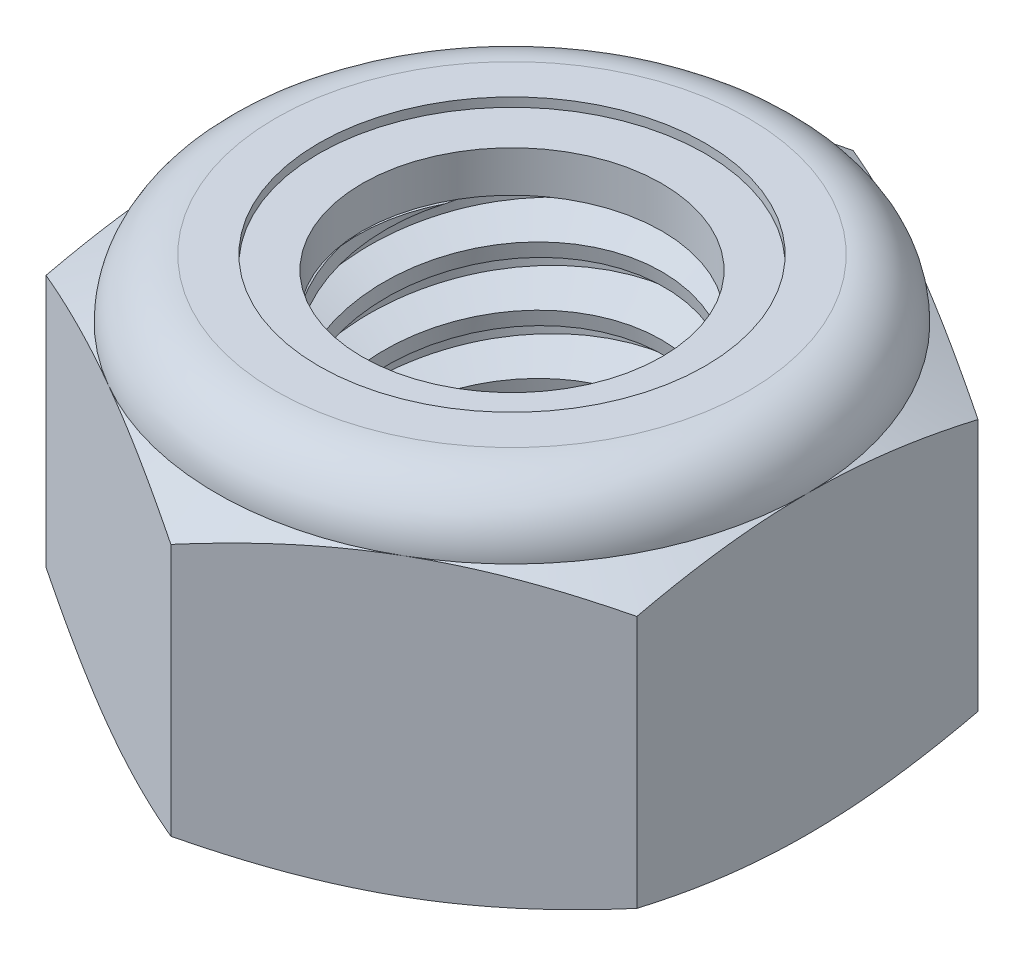
SolidWorks part; units mm, degrees
ref_plane "Front" through (0, 0, 0) normal (0, 0, 1) x (1, 0, 0)
ref_plane "Top" through (0, 0, 0) normal (0, 1, 0) x (1, 0, 0)
ref_plane "Right" through (0, 0, 0) normal (1, 0, 0) x (0, 0, -1)
sketch "Sketch1" plane through (0, 0, 0) normal (0, 1, 0) x (1, 0, 0)
  line L1 (0, 5.7735) -> (-5, 2.8868)
  line L2 (-5, 2.8868) -> (-5, -2.8868)
  line L3 (-5, -2.8868) -> (0, -5.7735)
  line L4 (0, -5.7735) -> (5, -2.8868)
  line L5 (5, -2.8868) -> (5, 2.8868)
  line L6 (5, 2.8868) -> (0, 5.7735)
  circle A0 centre (0, 0) radius 5 construction
  dimension "Hex Flats" = 10
extrude "Extrude1" add sketch "Sketch1" along normal blind 6
sketch "Sketch2" plane through (0, 0, 0) normal (1, 0, 0) x (0, 0, -1)
  line L0 (-3, 0) -> (-3, 6) construction
  line L1 (0, 0) -> (3, 0)
  line L2 (0, 0) -> (0, 6)
  line L3 (0, 6) -> (3, 6)
  line L4 (3, 0) -> (3, 6)
  line L5 (-2.8868, 6) -> (2.8868, 6) construction
  line L7 (0, -3) -> (0, 0) construction
  dimension "Thread Dia" = 6
revolve "Revolve1" add sketch "Sketch2" angle 360 about L7
sketch "Sketch3" plane through (0, 0, 0) normal (1, 0, 0) x (0, 0, -1)
  line L0 (3, 6) -> (-3, 6) construction
  line L1 (-3, 6) -> (-3, 5) construction
  line L2 (-3, 5) -> (3, 6) construction
  line L3 (3, 6) -> (3.0205, 5.8767) construction
  line L4 (3.0205, 5.8767) -> (3.1644, 5.0136)
  line L5 (3.1644, 5.0136) -> (2.5791, 5.2329)
  line L6 (2.5791, 5.2329) -> (2.538, 5.4795)
  line L7 (2.538, 5.4795) -> (3.0205, 5.8767)
  line L8 (2.5586, 5.3562) -> (3.0925, 5.4452) construction
  line L9 (3, 6) -> (3, 5.4297) construction
  line L10 (3, 5.4297) -> (-3, 4.4297) construction
  line L11 (-3, 4.4297) -> (-3, 5) construction
  line L12 (-0.1784, 6) -> (0.1784, 3.8595) construction
  line L13 (-3, 0) -> (-3, 6) construction
  line L14 (0, 6) -> (3, 6) construction
  line L15 (3, 0) -> (3, 6) construction
  point P13 (0, 4.9297)
  dimension "D1" = 0.125
  dimension "D2" = 0.25
  dimension "Thread Pitch" = 1
  dimension "D4" = 60
  dimension "D5" = 1
revolve "Cut-Revolve1" cut sketch "Sketch3" angle 360 about L12
pattern_linear "LPattern1" count 6 spacing 1 along (0, -1, 0) count 2 spacing 1 along (0, 1, 0) of "Cut-Revolve1"
sketch "Sketch4" plane through (0, 0, 0) normal (1, 0, 0) x (0, 0, -1)
  line L0 (0, 6) -> (3, 6)
  line L1 (3, 6) -> (2.538, 5.7846)
  line L2 (2.538, 5.7846) -> (2.538, 0.2154)
  line L3 (2.538, 0.2154) -> (3, 0)
  line L4 (3, 0) -> (0, 0)
  line L5 (0, 0) -> (0, 6)
  line L6 (3, 0) -> (3, 6) construction
  line L7 (0, 6) -> (3, 6) construction
  line L8 (0, 0) -> (3, 0) construction
  line L9 (0, 0) -> (0, 6) construction
  line L10 (0, 6) -> (0, 6.5097) construction
  dimension "D1" = 25
revolve "Cut-Revolve2" cut sketch "Sketch4" angle 360 about L10
combine bodies "Combine1" operation type subtract main body 112 bodies to subtract 111
sketch "Sketch5" plane through (0, 0, 0) normal (1, 0, 0) x (0, 0, -1)
  line L0 (0, 0) -> (5, 0)
  line L1 (5, 0) -> (5.7735, 0.3607)
  line L2 (5.7735, 0.3607) -> (5.7735, 4.6393)
  line L3 (5.7735, 4.6393) -> (5, 5)
  line L4 (4, 6) -> (4, 7.27)
  line L5 (4, 7.27) -> (7.0435, 7.27)
  line L6 (7.0435, 7.27) -> (7.0435, -1.27)
  line L7 (7.0435, -1.27) -> (0, -1.27)
  line L8 (0, -1.27) -> (0, 0)
  line L9 (5, 5) -> (5, 0) construction
  line L10 (0, 0) -> (3, 0) construction
  line L13 (5.7735, 2.5) -> (7.0435, 2.5) construction
  line L14 (5.7735, 6) -> (5.7735, 0) construction
  line L15 (0, 0) -> (0, 7.27) construction
  line L20 (0, 7.27) -> (4, 7.27) construction
  line L22 (0, 6) -> (3, 6) construction
  arc A0 (5, 5) -> (4, 6) centre (4, 5) ccw
  dimension "D1" = 25
  dimension "D2" = 1.27
  dimension "D3" = 6
  dimension "D4" = 1
revolve "Cut-Revolve3" cut sketch "Sketch5" angle 360 about L15
sketch "Sketch6" plane through (0, 0, 0) normal (1, 0, 0) x (0, 0, -1)
  line L0 (0, 5) -> (4.8476, 5)
  line L1 (4, 5.8476) -> (3.269, 5.8476)
  line L2 (0, 7.27) -> (0, 5)
  line L3 (3.269, 7.27) -> (0, 7.27)
  line L4 (0, 7.27) -> (4, 7.27) construction
  line L5 (0, 0) -> (0, 7.27) construction
  line L6 (0, 7.27) -> (0, 44.323) construction
  line L7 (3.269, 5.8476) -> (3.269, 7.27)
  line L8 (4, 6) -> (4, 5.8476) construction
  line L9 (3.269, 5.8476) -> (2.538, 5.8476) construction
  line L10 (2.538, 5.8476) -> (2.538, 5.7846) construction
  arc A0 (4.8476, 5) -> (4, 5.8476) centre (4, 5) ccw
  arc A1 (5, 5) -> (4, 6) centre (4, 5) ccw construction
  dimension "D1" = 0.1524
revolve "Cut-Revolve4" cut sketch "Sketch6" angle 360 about L6
sketch "Sketch7" plane through (0, 0, 0) normal (1, 0, 0) x (0, 0, -1)
  line L0 (2.538, 5.0762) -> (4.7676, 5.0762)
  line L1 (4, 5.7714) -> (2.538, 5.7714)
  line L2 (2.538, 5.7714) -> (2.538, 5.0762)
  line L3 (2.538, 5.0762) -> (0, 5.0762) construction
  line L4 (0, 5.0762) -> (0, 5.7714) construction
  line L5 (0, 5.7714) -> (2.538, 5.7714) construction
  line L6 (2.538, 5.0762) -> (2.538, 5) construction
  line L7 (0, 5) -> (4.8476, 5) construction
  line L8 (4, 5.7714) -> (4, 5.8476) construction
  arc A0 (4.7676, 5.0762) -> (4, 5.7714) centre (4, 5) ccw
  arc A2 (4.8476, 5) -> (4, 5.8476) centre (4, 5) ccw construction
  dimension "D1" = 0.0762
revolve "Revolve2" add sketch "Sketch7" angle 360 about L4
equation "\"D1@Sketch3\"=\"Thread Pitch@Sketch3\"/8"
equation "\"D2@Sketch3\"=\"Thread Pitch@Sketch3\"/4"
equation "\"D5@Sketch3\"=\"Thread Pitch@Sketch3\""
equation "\"D4@LPattern1\"=\"Thread Pitch@Sketch3\""
equation "\"D3@LPattern1\"=\"Thread Pitch@Sketch3\""
equation "\"D1@LPattern1\"=\"Height@Extrude1\"/\"Thread Pitch@Sketch3\""
equation "\"D4@Sketch5\"=\"Height@Extrude1\"/6"
